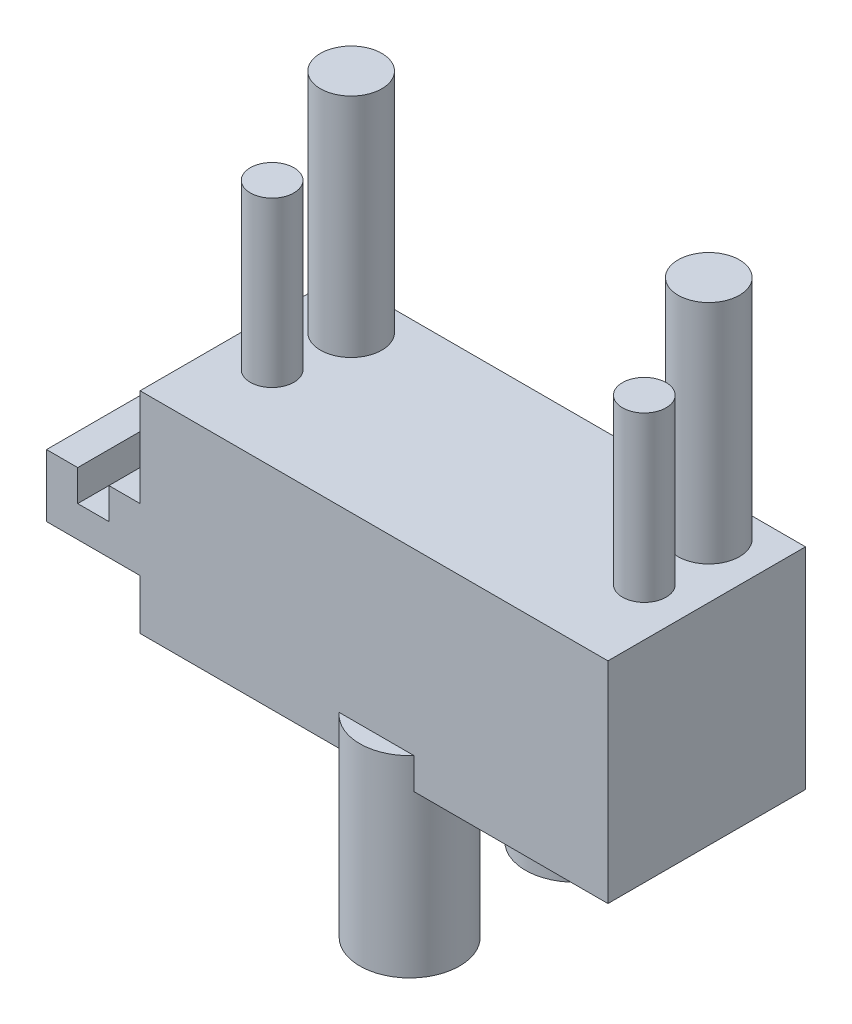
SolidWorks part; units mm, degrees
ref_plane "Front Plane" through (0, 0, 0) normal (0, 0, 1) x (1, 0, 0)
ref_plane "Top Plane" through (0, 0, 0) normal (0, 1, 0) x (1, 0, 0)
ref_plane "Right Plane" through (0, 0, 0) normal (1, 0, 0) x (0, 0, -1)
sketch "Sketch1" plane through (0, 0, 0) normal (0, 1, 0) x (1, 0, 0)
  line L1 (-40.1858, -24.5795) -> (-17.6858, -24.5795)
  line L2 (-40.1858, -24.5795) -> (-40.1858, -17.5795)
  line L3 (-40.1858, -17.5795) -> (-17.6858, -17.5795)
  line L4 (-17.6858, -24.5795) -> (-17.6858, -17.5795)
  dimension "D1" = 22.5
  dimension "D2" = 7
extrude "Boss-Extrude1" add sketch "Sketch1" along normal blind 1.5
sketch "Sketch2" plane through (0, 1.5, 0) normal (0, 1, 0) x (1, 0, 0)
  line L0 (-17.6858, -24.5795) -> (-17.6858, -17.5795) construction
  line L2 (-40.1858, -24.5795) -> (-17.6858, -24.5795) construction
  circle A0 centre (-37.5358, -19.5795) radius 1.475
  circle A1 centre (-20.3358, -19.5795) radius 1.475
  dimension "D1" = 2.95
  dimension "D2" = 2.95
  dimension "D3" = 17.2
  dimension "D4" = 2.65
  dimension "D5" = 5
  dimension "D6" = 5
extrude "Boss-Extrude2" add sketch "Sketch2" along normal blind 13.5
sketch "Sketch3" plane through (0, 1.5, 0) normal (0, 1, 0) x (1, 0, 0)
  circle A0 centre (-37.8858, -23.0295) radius 1.05
  circle A1 centre (-19.9858, -23.0295) radius 1.05
  circle A2 centre (-37.5358, -19.5795) radius 1.475 construction
  circle A3 centre (-20.3358, -19.5795) radius 1.475 construction
  dimension "D1" = 2.1
  dimension "D2" = 2.1
  dimension "D3" = 0.35
  dimension "D4" = 0.35
  dimension "D5" = 3.45
  dimension "D6" = 3.45
extrude "Boss-Extrude3" add sketch "Sketch3" along normal blind 10.5
sketch "Sketch4" plane through (0, 0, 0) normal (0, -1, 0) x (-1, 0, 0)
  line L0 (40.1858, -17.5795) -> (40.1858, -24.5795) construction
  line L1 (17.6858, -24.5795) -> (40.1858, -24.5795)
  line L2 (17.6858, -24.5795) -> (17.6858, -27.0795)
  line L3 (17.6858, -27.0795) -> (40.1858, -27.0795)
  line L4 (40.1858, -24.5795) -> (40.1858, -27.0795)
  line L6 (20.9358, -27.0795) -> (23.9358, -27.0795)
  line L7 (20.9358, -27.0795) -> (20.9358, -29.9823)
  line L8 (20.9358, -29.9823) -> (23.9358, -29.9823)
  line L9 (23.9358, -27.0795) -> (23.9358, -29.9823)
  line L10 (32.4358, -27.0795) -> (35.4358, -27.0795)
  line L11 (32.4358, -27.0795) -> (32.4358, -28.8632)
  line L12 (32.4358, -28.8632) -> (35.4358, -28.8632)
  line L13 (35.4358, -27.0795) -> (35.4358, -28.8632)
  line M13 (40.1858, -24.5795) -> (40.1858, -17.5795)
  line M14 (40.1858, -17.5795) -> (17.6858, -17.5795)
  line M15 (17.6858, -17.5795) -> (17.6858, -24.5795)
  line M16 (17.6858, -24.5795) -> (40.1858, -24.5795)
  dimension "D1" = 0
  dimension "D2" = 3.25
  dimension "D3" = 4.75
  dimension "D4" = 2.5
  dimension "D5" = 3
  dimension "D6" = 3
extrude "Boss-Extrude4" add sketch "Sketch4" along normal blind 6 and the other way blind 1.5 contours L4 L2 L3 M16 | M16 M13 M14 M15
sketch "Sketch8" plane through (0, 1.5, 0) normal (0, 1, 0) x (1, 0, 0)
  line L1 (-40.1858, -17.5795) -> (-17.6858, -17.5795)
  line L2 (-40.1858, -17.5795) -> (-40.1858, -27.0795)
  line L3 (-40.1858, -27.0795) -> (-17.6858, -27.0795)
  line L4 (-17.6858, -17.5795) -> (-17.6858, -27.0795)
extrude "Boss-Extrude7" add sketch "Sketch8" along normal blind 2.61
sketch "Sketch9" plane through (0, -6, 0) normal (0, -1, 0) x (-1, 0, 0)
  line L0 (17.6858, -17.5795) -> (17.6858, -27.0795) construction
  line L3 (17.6858, -27.0795) -> (40.1858, -27.0795) construction
  circle A0 centre (28.8108, -25.4895) radius 2.4
  circle A1 centre (28.8108, -17.5195) radius 2.4
  dimension "D1" = 11.125
  dimension "D2" = 11.125
  dimension "D3" = 4.8
  dimension "D4" = 4.8
  dimension "D5" = 1.59
  dimension "D6" = 7.97
extrude "Boss-Extrude8" add sketch "Sketch9" along normal blind 7.76 and the other way blind 1.5
sketch "Sketch10" plane through (0, -6, 0) normal (0, -1, 0) x (-1, 0, 0)
  line L1 (40.1858, -27.0795) -> (17.6858, -27.0795)
  line L2 (40.1858, -27.0795) -> (40.1858, -17.5795)
  line L3 (40.1858, -17.5795) -> (17.6858, -17.5795)
  line L4 (17.6858, -27.0795) -> (17.6858, -17.5795)
sketch "Sketch11" plane through (-17.6858, 0, 0) normal (1, 0, 0) x (0, 0, -1)
  line L0 (-27.0795, 4.11) -> (-17.5795, 4.11) construction
  line L1 (-17.5795, -0.59) -> (-27.0795, -0.59)
  line L2 (-17.5795, -0.59) -> (-17.5795, -3.59)
  line L3 (-17.5795, -3.59) -> (-27.0795, -3.59)
  line L4 (-27.0795, -0.59) -> (-27.0795, -3.59)
  line L5 (-17.5795, 4.11) -> (-17.5795, -6) construction
  line L6 (-27.0795, 4.11) -> (-27.0795, -6) construction
  point P8 (-17.5795, -0.945)
  dimension "D1" = 4.7
  dimension "D2" = 0
  dimension "D3" = 0
  dimension "D4" = 3
sketch "Sketch15" plane through (-40.1858, 0, 0) normal (-1, 0, 0) x (0, 0, 1)
  line L0 (27.0795, 4.11) -> (27.0795, -6) construction
  line L1 (27.0795, -0.59) -> (17.5795, -0.59)
  line L2 (27.0795, -0.59) -> (27.0795, -3.59)
  line L3 (27.0795, -3.59) -> (17.5795, -3.59)
  line L4 (17.5795, -0.59) -> (17.5795, -3.59)
  line L5 (17.5795, 4.11) -> (17.5795, -6) construction
  line L6 (17.5795, 4.11) -> (27.0795, 4.11) construction
  dimension "D1" = 3
  dimension "D2" = 4.7
extrude "Boss-Extrude11" add sketch "Sketch15" along normal blind 4.5
sketch "Sketch16" plane through (0, -0.59, 0) normal (0, 1, 0) x (1, 0, 0)
  line L0 (-44.6858, -27.0795) -> (-40.1858, -27.0795) construction
  line L1 (-41.6858, -27.0795) -> (-43.1858, -27.0795)
  line L2 (-41.6858, -27.0795) -> (-41.6858, -17.5795)
  line L3 (-41.6858, -17.5795) -> (-43.1858, -17.5795)
  line L4 (-43.1858, -27.0795) -> (-43.1858, -17.5795)
  line L5 (-44.6858, -17.5795) -> (-40.1858, -17.5795) construction
  line L6 (-44.6858, -27.0795) -> (-44.6858, -17.5795) construction
  line L7 (-40.1858, -27.0795) -> (-40.1858, -17.5795) construction
  point P8 (-39.6503, -23.2619)
  dimension "D1" = 1.5
  dimension "D2" = 1.5
extrude "Cut-Extrude3" cut sketch "Sketch16" against normal blind 1.5
